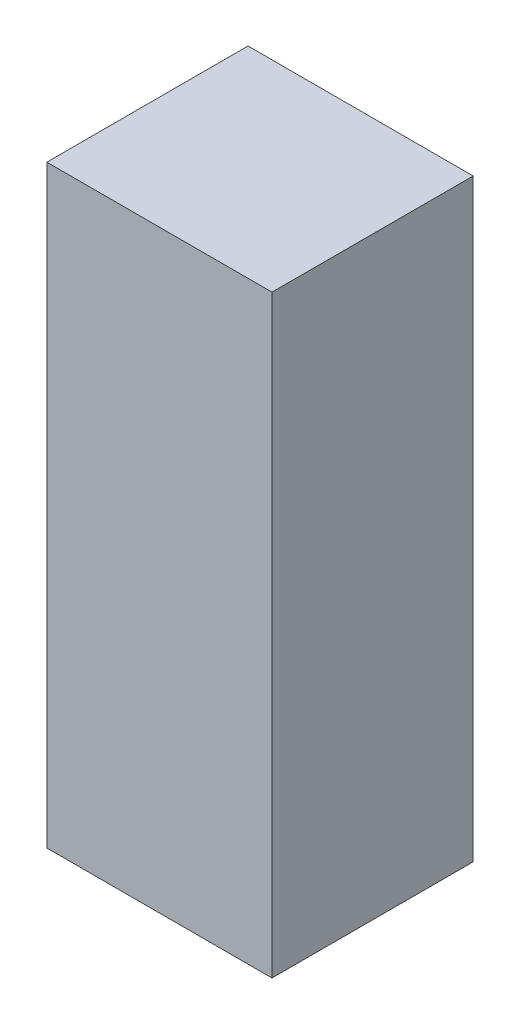
SolidWorks part; units mm, degrees
ref_plane "Front Plane" through (0, 0, 0) normal (0, 0, 1) x (1, 0, 0)
ref_plane "Top Plane" through (0, 0, 0) normal (0, 1, 0) x (1, 0, 0)
ref_plane "Right Plane" through (0, 0, 0) normal (1, 0, 0) x (0, 0, -1)
sketch "Sketch1" plane through (0, 0, 0) normal (0, 1, 0) x (1, 0, 0)
  line L1 (0, 0) -> (596.9, 0)
  line L2 (0, 0) -> (0, 533.4)
  line L3 (0, 533.4) -> (596.9, 533.4)
  line L4 (596.9, 0) -> (596.9, 533.4)
  dimension "D1" = 533.4
  dimension "D2" = 596.9
extrude "Boss-Extrude1" add sketch "Sketch1" along normal blind 1574.8
